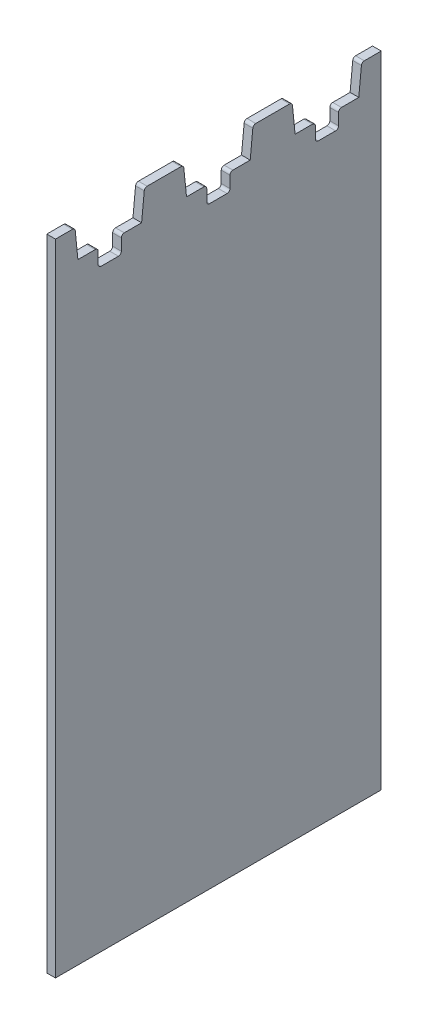
SolidWorks part; units mm, degrees
ref_plane "Front Plane" through (0, 0, 0) normal (0, 0, 1) x (1, 0, 0)
ref_plane "Top Plane" through (0, 0, 0) normal (0, 1, 0) x (1, 0, 0)
ref_plane "Right Plane" through (0, 0, 0) normal (1, 0, 0) x (0, 0, -1)
sketch "Sketch2" plane through (0, 0, 0) normal (1, 0, 0) x (0, 0, -1)
  line L0 (-18.75, 103) -> (-18.75, 118)
  line L1 (-18.75, -103) -> (18.75, -103)
  line L2 (-18.75, -103) -> (-18.75, 103)
  line L3 (-18.75, 103) -> (18.75, 103)
  line L4 (18.75, -103) -> (18.75, 103)
  line L5 (-18.75, -103) -> (18.75, 103) construction
  line L6 (-18.75, 103) -> (18.75, -103) construction
  line L7 (-18.75, 118) -> (-12, 118)
  line L8 (-12, 118) -> (-11, 108)
  line L9 (-11, 108) -> (11, 108)
  line L10 (11, 108) -> (12, 118)
  line L11 (12, 118) -> (18.75, 118)
  line L12 (18.75, 118) -> (18.75, 103)
  line L13 (-12, 118) -> (-12, 108) construction
  line L14 (-12, 108) -> (-11, 108) construction
  line L15 (11, 108) -> (12, 108) construction
  line L16 (12, 108) -> (12, 118) construction
  line L17 (-18.75, 118) -> (-18.75, 125) construction
  line L18 (-18.75, 125) -> (18.75, 125) construction
  line L19 (18.75, 125) -> (18.75, 118) construction
  line L20 (0, 105) -> (0, 108) construction
  line L21 (-4, 102) -> (4, 102)
  line L22 (-4, 102) -> (-4, 108)
  line L23 (-4, 108) -> (4, 108)
  line L24 (4, 102) -> (4, 108)
  line L25 (-4, 102) -> (4, 108) construction
  line L26 (-4, 108) -> (4, 102) construction
  point P0 (0, 0)
  point P7 (0, 105)
  point P21 (0, 108)
  dimension "D1" = 206
  dimension "D2" = 37.5
  dimension "D3" = 22
  dimension "D4" = 10
  dimension "D5" = 1
  dimension "D6" = 7
  dimension "D7" = 228
  dimension "D8" = 6
  dimension "D9" = 8
extrude "Boss-Extrude2" add sketch "Sketch2" along normal blind 3 contours L1 L4 L3 L2 | L24 L3 L12 L11 L10 L9 | L3 L22 L9 L8 L7 L0
fillet "Fillet1" radius 1 6 edges at (1.5, 118, -12) (1.5, 118, 12) (1.5, 102, -4) (1.5, 108, -4) (1.5, 108, 4) (1.5, 102, 4)
pattern_linear "LPattern1" count 3 spacing 37.5 along (0, 0, 1) of "Boss-Extrude2", "Fillet1"
